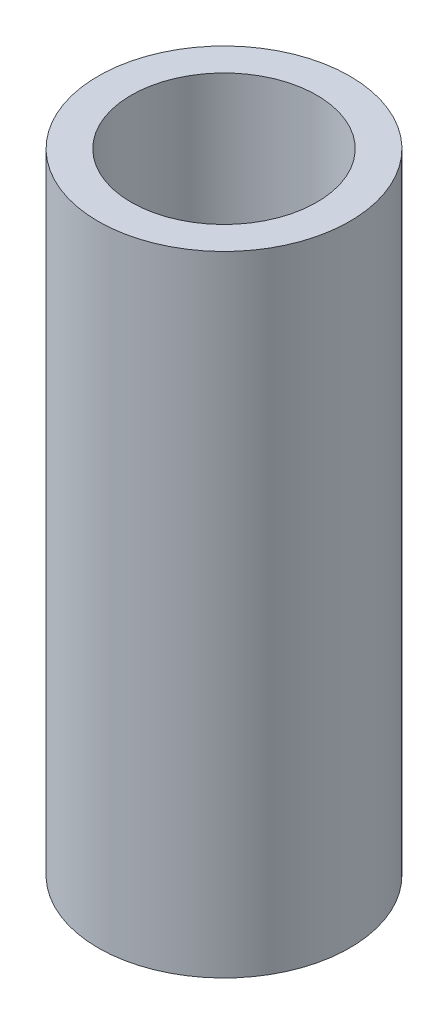
SolidWorks part; units mm, degrees
ref_plane "Front Plane" through (0, 0, 0) normal (0, 0, 1) x (1, 0, 0)
ref_plane "Top Plane" through (0, 0, 0) normal (0, 1, 0) x (1, 0, 0)
ref_plane "Right Plane" through (0, 0, 0) normal (1, 0, 0) x (0, 0, -1)
sketch "Sketch1" plane through (0, 0, 0) normal (0, 1, 0) x (1, 0, 0)
  circle A0 centre (0, 0) radius 2.95
  circle A1 centre (0, 0) radius 4
  dimension "D1" = 5.9
  dimension "D2" = 8
extrude "Boss-Extrude1" add sketch "Sketch1" along normal blind 20
